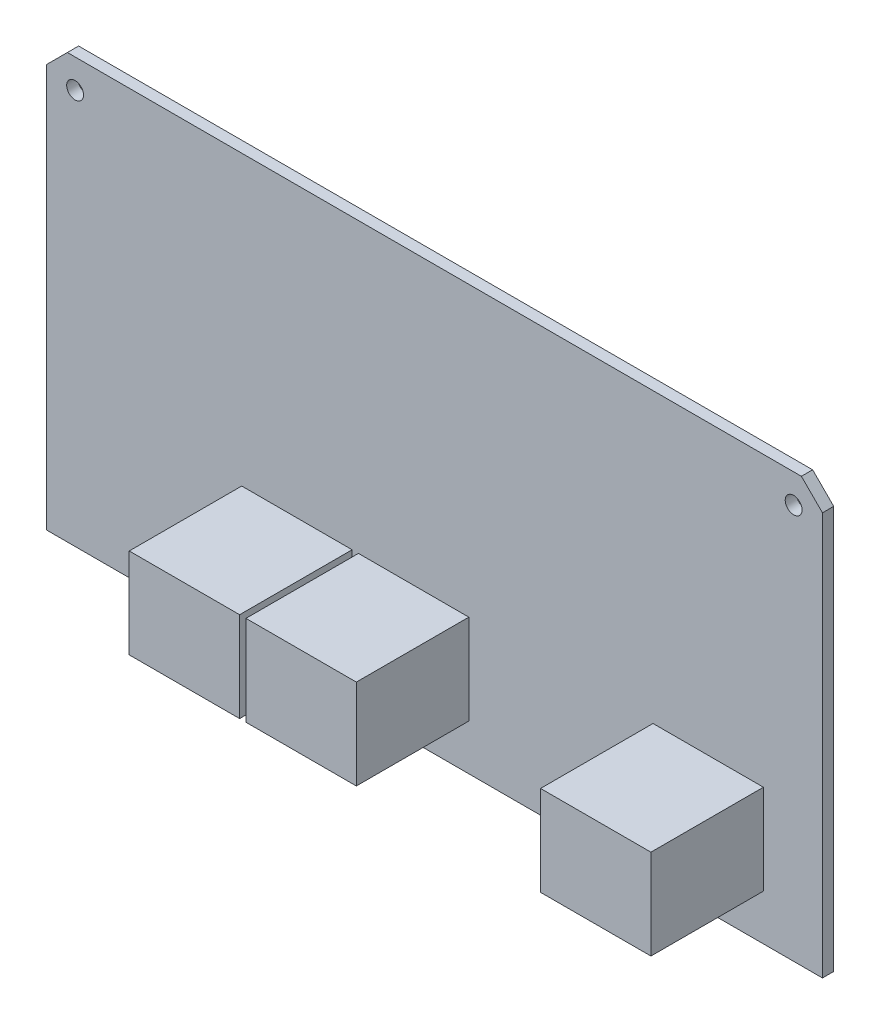
SolidWorks part; units mm, degrees
ref_plane "Alzado" through (0, 0, 0) normal (0, 0, 1) x (1, 0, 0)
ref_plane "Planta" through (0, 0, 0) normal (0, 1, 0) x (1, 0, 0)
ref_plane "Vista lateral" through (0, 0, 0) normal (1, 0, 0) x (0, 0, -1)
sketch "Croquis1" plane through (0, 0, 0) normal (0, 0, 1) x (1, 0, 0)
  line L0 (-55.2, 26.05) -> (-51.1, 26.05) construction
  line L1 (55.2, -30.15) -> (-55.2, -30.15)
  line L2 (55.2, -30.15) -> (55.2, 27.15)
  line L3 (52.2, 30.15) -> (-52.2, 30.15)
  line L4 (-55.2, -30.15) -> (-55.2, 27.15)
  line L5 (55.2, -30.15) -> (-55.2, 30.15) construction
  line L6 (55.2, 30.15) -> (-55.2, -30.15) construction
  line L7 (-51.1, 26.05) -> (51.1, 26.05) construction
  line L8 (51.1, 26.05) -> (55.2, 26.05) construction
  line L9 (55.2, 27.15) -> (52.2, 30.15)
  line L10 (-52.2, 30.15) -> (-55.2, 27.15)
  circle A0 centre (-51.1, 26.05) radius 1.2
  circle A1 centre (51.1, 26.05) radius 1.2
  point P0 (0, 0)
  point P12 (-51.1, 27.25)
  point P13 (-52.3, 26.05)
  dimension "D3" = 2.4
  dimension "D1" = 60.3
  dimension "D2" = 110.4
  dimension "D4" = 2.9
  dimension "D5" = 2.9
  dimension "D8" = 3
  dimension "D9" = 3
extrude "Saliente-Extruir1" add sketch "Croquis1" along normal blind 1.6
sketch "Croquis2" plane through (0, 0, 1.6) normal (0, 0, 1) x (1, 0, 0)
  line L0 (-55.2, -23.65) -> (55.2, -23.65) construction
  line L1 (-55.2, 27.15) -> (-55.2, -30.15) construction
  line L2 (55.2, -30.15) -> (55.2, 27.15) construction
  line L3 (-55.2, -30.15) -> (55.2, -30.15) construction
  line L4 (-27.4, -23.65) -> (-11.7, -23.65)
  line L5 (-27.4, -23.65) -> (-27.4, -10.85)
  line L6 (-27.4, -10.85) -> (-11.7, -10.85)
  line L7 (-11.7, -23.65) -> (-11.7, -10.85)
  line L8 (-10.8, -23.65) -> (4.9, -23.65)
  line L9 (-10.8, -23.65) -> (-10.8, -10.85)
  line L10 (-10.8, -10.85) -> (4.9, -10.85)
  line L11 (4.9, -23.65) -> (4.9, -10.85)
  line L12 (31.1, -23.65) -> (46.8, -23.65)
  line L13 (31.1, -23.65) -> (31.1, -10.85)
  line L14 (31.1, -10.85) -> (46.8, -10.85)
  line L15 (46.8, -23.65) -> (46.8, -10.85)
  dimension "D1" = 15.7
  dimension "D2" = 12.8
  dimension "D3" = 8.4
  dimension "D4" = 26.2
  dimension "D5" = 27.8
  dimension "D6" = 6.5
extrude "Saliente-Extruir2" add sketch "Croquis2" along normal blind 16
